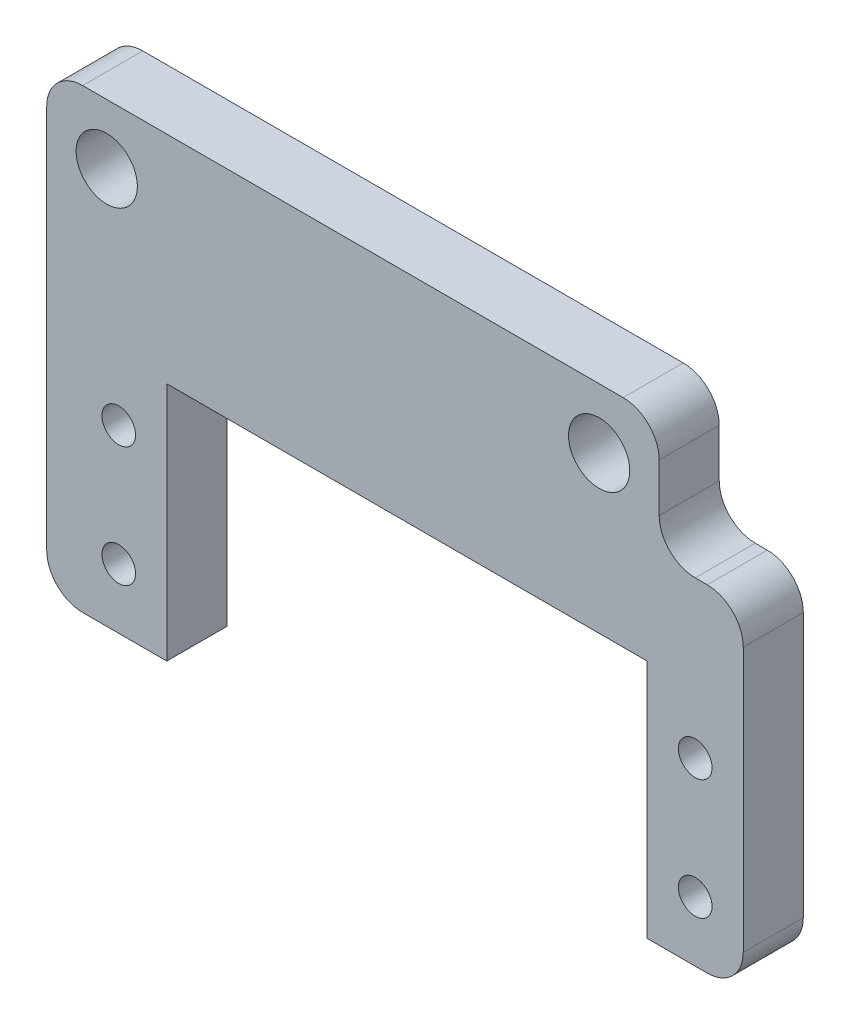
SolidWorks part; units mm, degrees
ref_plane "Front Plane" through (0, 0, 0) normal (0, 0, 1) x (1, 0, 0)
ref_plane "Top Plane" through (0, 0, 0) normal (0, 1, 0) x (1, 0, 0)
ref_plane "Right Plane" through (0, 0, 0) normal (1, 0, 0) x (0, 0, -1)
sketch "Sketch1" plane through (0, 0, 0) normal (0, 0, 1) x (1, 0, 0)
  line L0 (0, 5) -> (51, 5) construction
  line L1 (0, 0) -> (51, 0)
  line L2 (0, 0) -> (0, 10)
  line L3 (0, 10) -> (51, 10)
  line L4 (51, 0) -> (51, 10)
  circle A0 centre (5, 5) radius 2.55
  circle A1 centre (46, 5) radius 2.55
  point P11 (37.0723, 5)
  point P12 (3.8437, 5)
  dimension "D5" = 5.1
  dimension "D1" = 10
  dimension "D2" = 41
  dimension "D3" = 5
  dimension "D4" = 5
extrude "Boss-Extrude1" add sketch "Sketch1" along normal blind 5
sketch "Sketch2" plane through (0, 0, 5) normal (0, 0, 1) x (1, 0, 0)
  line L0 (0, 10) -> (0, 0) construction
  line L1 (10, -28) -> (50, -28) construction
  line L2 (10, -28) -> (10, -8)
  line L3 (10, -8) -> (50, -8)
  line L4 (50, -28) -> (50, -8)
  line L5 (0, 0) -> (51, 0) construction
  line L6 (10, -28) -> (0, -28)
  line L7 (0, -28) -> (0, 0)
  line L8 (0, 0) -> (51, 0)
  line L9 (51, 0) -> (58, 0)
  line L10 (58, 0) -> (58, -28)
  line L11 (58, -28) -> (50, -28)
  line L12 (6, -28) -> (6, 0) construction
  line L13 (30, -8) -> (30, -28) construction
  circle A0 centre (6, -23) radius 1.4
  circle A1 centre (6, -13) radius 1.4
  circle A2 centre (54, -23) radius 1.4
  circle A3 centre (54, -13) radius 1.4
  dimension "D9" = 2.8
  dimension "D1" = 40
  dimension "D2" = 20
  dimension "D3" = 10
  dimension "D4" = 8
  dimension "D5" = 8
  dimension "D6" = 4
  dimension "D7" = 10
  dimension "D8" = 5
extrude "Boss-Extrude2" add sketch "Sketch2" against normal blind 5
fillet "Fillet1" radius 3 6 edges at (0, -28, 2.5) (58, -28, 2.5) (58, 0, 2.5) (0, 10, 2.5) (51, 10, 2.5) (51, 0, 2.5)
